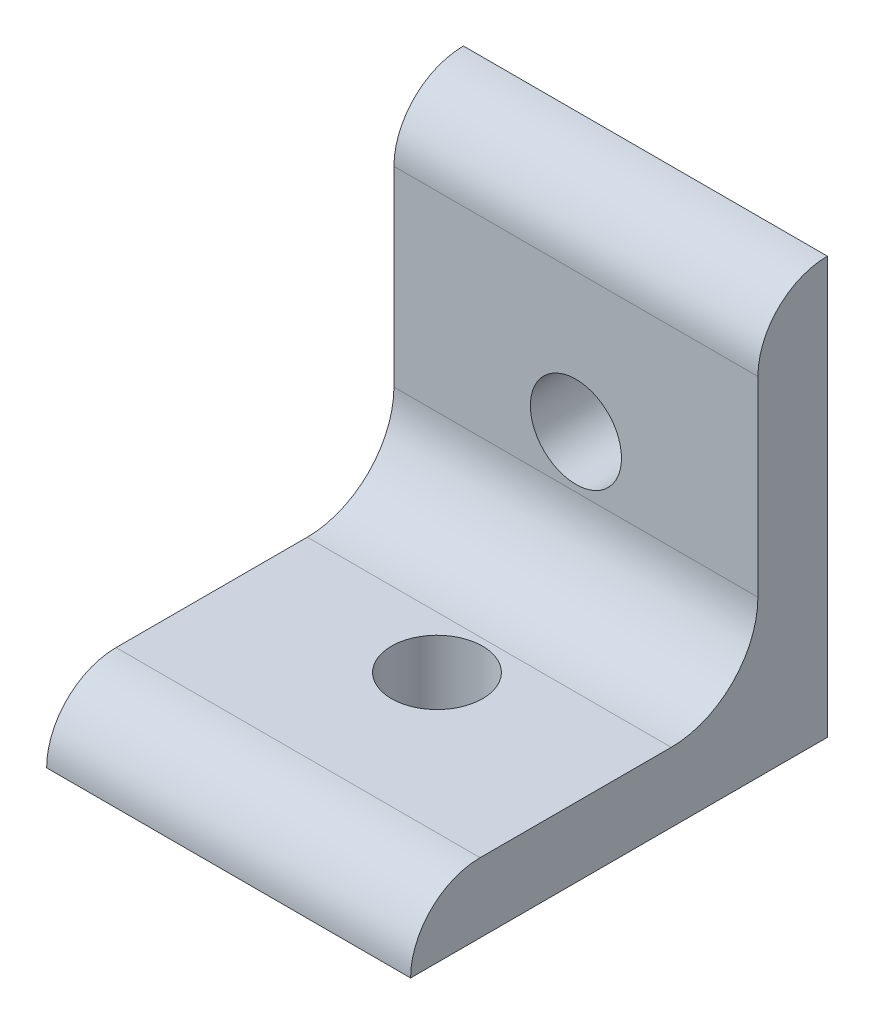
SolidWorks part; units mm, degrees
ref_plane "Front Plane" through (0, 0, 0) normal (0, 0, 1) x (1, 0, 0)
ref_plane "Top Plane" through (0, 0, 0) normal (0, 1, 0) x (1, 0, 0)
ref_plane "Right Plane" through (0, 0, 0) normal (1, 0, 0) x (0, 0, -1)
ref_plane "Plane1" through (16.637, 0, 0) normal (1, 0, 0) x (0, 0, -1)
sketch "Sketch1" plane through (16.637, 0, 0) normal (1, 0, 0) x (0, 0, -1)
  line L0 (-38.1, 0) -> (0, 0)
  line L1 (0, 0) -> (0, 38.1)
  line L2 (-6.35, 31.75) -> (-6.35, 6.35)
  line L3 (-6.35, 6.35) -> (-31.75, 6.35)
  arc A0 (-31.75, 6.35) -> (-38.1, 0) centre (-31.75, 0) ccw
  arc A1 (0, 38.1) -> (-6.35, 31.75) centre (0, 31.75) ccw
extrude "Boss-Extrude1" add sketch "Sketch1" against normal blind 33.274
hole_wizard "Hole1" positions "Sketch3" profile "Sketch2" legacy
sketch "Sketch3" plane through (0, 0, 6.35) normal (0, 0, 1) x (1, 0, 0)
  point P0 (0, 19.05)
sketch "Sketch2" plane through (0, 19.05, 6.35) normal (1, 0, 0) x (0, -1, 0)
  line L0 (0, 0) -> (0, 6.35)
  line L1 (0, 6.35) -> (4.1656, 6.35)
  line L2 (4.1656, 6.35) -> (4.1656, 0)
  line L3 (4.1656, 0) -> (0, 0)
  line L4 (0, 110) -> (0, -10) construction
  dimension "Diameter" = 8.3312
  dimension "Depth" = 6.35
hole_wizard "Hole2" positions "Sketch5" profile "Sketch4" legacy
sketch "Sketch5" plane through (0, 6.35, 0) normal (0, 1, 0) x (1, 0, 0)
  point P0 (0, -19.05)
sketch "Sketch4" plane through (0, 6.35, 19.05) normal (1, 0, 0) x (0, 0, 1)
  line L0 (0, 0) -> (0, 6.35)
  line L1 (0, 6.35) -> (4.1656, 6.35)
  line L2 (4.1656, 6.35) -> (4.1656, 0)
  line L3 (4.1656, 0) -> (0, 0)
  line L4 (0, 110) -> (0, -10) construction
  dimension "Diameter" = 8.3312
  dimension "Depth" = 6.35
fillet "Fillet1" radius 7.9248 1 edges at (0, 6.35, 6.35)
